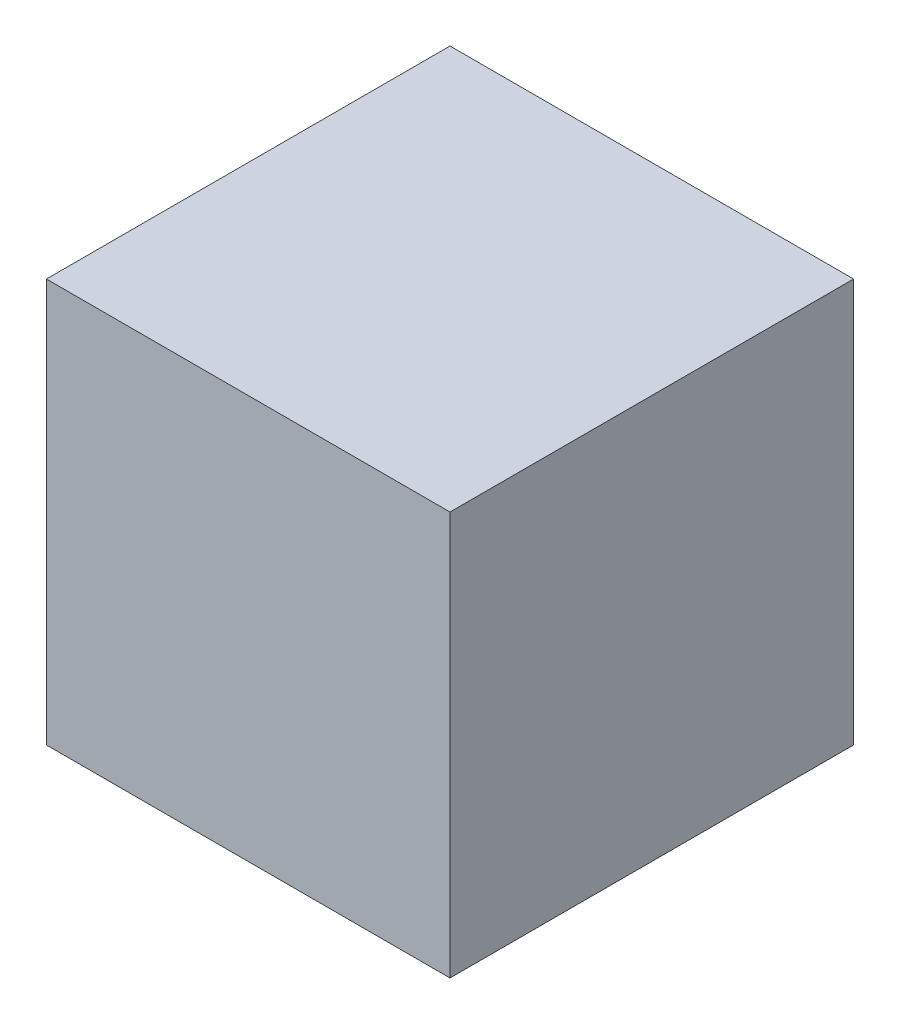
SolidWorks part; units mm, degrees
ref_plane "Front Plane" through (0, 0, 0) normal (0, 0, 1) x (1, 0, 0)
ref_plane "Top Plane" through (0, 0, 0) normal (0, 1, 0) x (1, 0, 0)
ref_plane "Right Plane" through (0, 0, 0) normal (1, 0, 0) x (0, 0, -1)
sketch "Sketch1" plane through (0, 0, 0) normal (0, 1, 0) x (1, 0, 0)
  line L1 (-12.7, 12.7) -> (12.7, 12.7)
  line L2 (-12.7, 12.7) -> (-12.7, -12.7)
  line L3 (-12.7, -12.7) -> (12.7, -12.7)
  line L4 (12.7, 12.7) -> (12.7, -12.7)
  line L5 (-12.7, 12.7) -> (12.7, -12.7) construction
  line L6 (-12.7, -12.7) -> (12.7, 12.7) construction
  point P0 (0, 0)
  dimension "D1" = 25.4
  dimension "D2" = 25.4
extrude "Boss-Extrude1" add sketch "Sketch1" along normal blind 25.4
